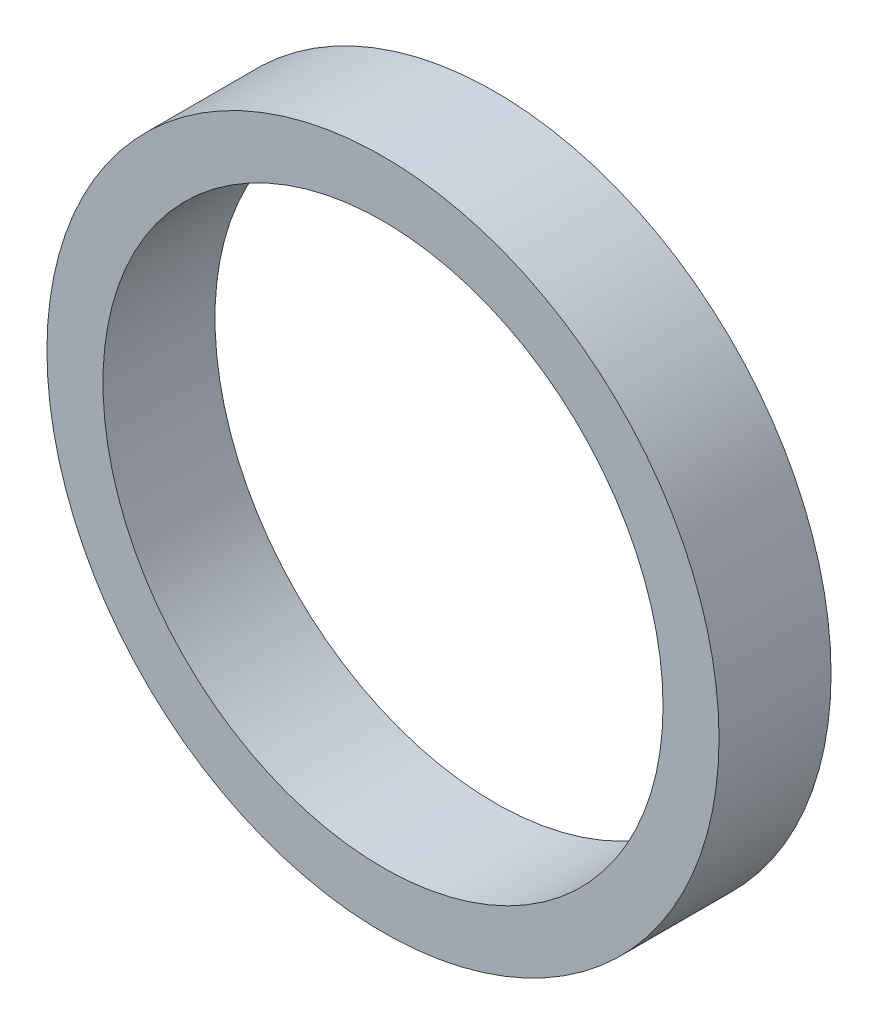
SolidWorks part; units mm, degrees
ref_plane "Front Plane" through (0, 0, 0) normal (0, 0, 1) x (1, 0, 0)
ref_plane "Top Plane" through (0, 0, 0) normal (0, 1, 0) x (1, 0, 0)
ref_plane "Right Plane" through (0, 0, 0) normal (1, 0, 0) x (0, 0, -1)
sketch "Sketch1" plane through (0, 0, 0) normal (0, 0, 1) x (1, 0, 0)
  circle A0 centre (0, 0) radius 25
  circle A1 centre (0, 0) radius 30
extrude "Boss-Extrude1" add sketch "Sketch1" along normal blind 10
